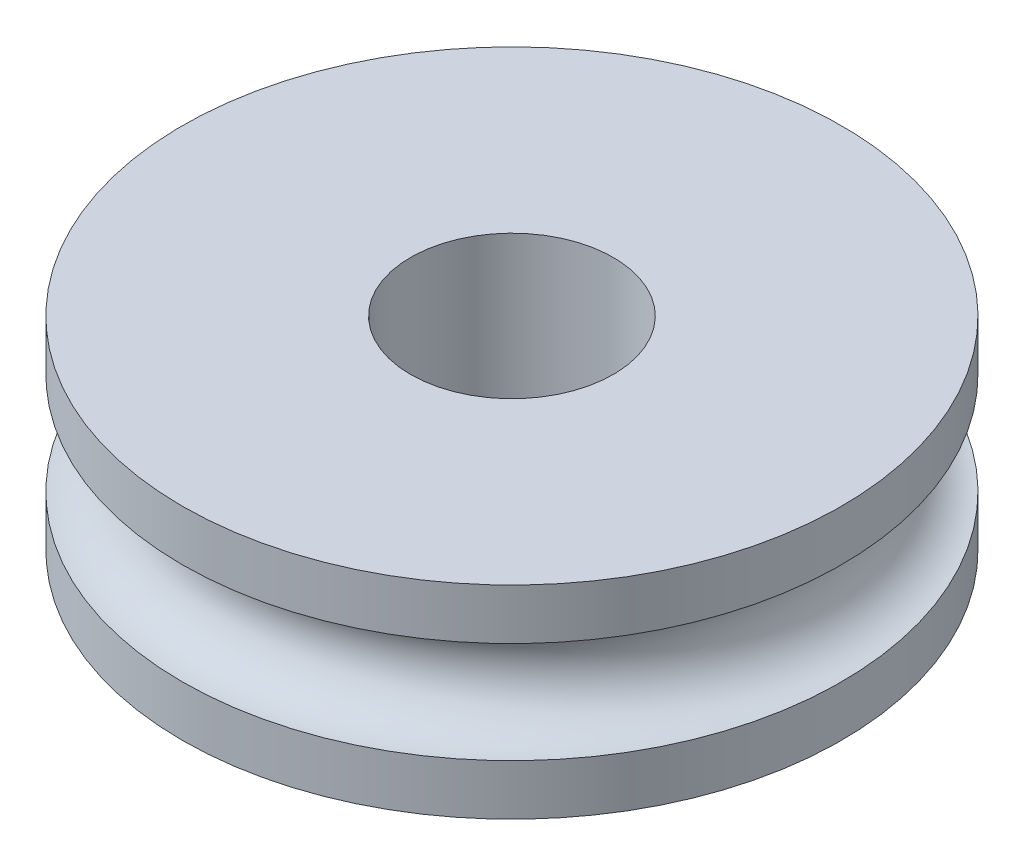
SolidWorks part; units mm, degrees
ref_plane "Front Plane" through (0, 0, 0) normal (0, 0, 1) x (1, 0, 0)
ref_plane "Top Plane" through (0, 0, 0) normal (0, 1, 0) x (1, 0, 0)
ref_plane "Right Plane" through (0, 0, 0) normal (1, 0, 0) x (0, 0, -1)
sketch "Sketch1" plane through (0, 0, 0) normal (0, 0, 1) x (1, 0, 0)
  line L0 (0, 2) -> (0, -2) construction
  line L1 (2, 2) -> (2, -2)
  line L2 (2, -2) -> (6.5, -2)
  line L3 (6.5, -2) -> (6.5, -1)
  line L4 (6.5, 1) -> (6.5, 2)
  line L5 (6.5, 2) -> (2, 2)
  line L6 (2, 0) -> (6.5, 0) construction
  line L7 (0, 0) -> (2, 0) construction
  arc A0 (6.5, -1) -> (6.5, 1) centre (6.5, 0) cw
  point P4 (0, 0)
  point P14 (0, 0)
  point P15 (3.1872, 0)
  dimension "D3" = 1
  dimension "D1" = 4
  dimension "D2" = 4
  dimension "D4" = 13
  dimension "D5" = 4
revolve "Revolve1" add sketch "Sketch1" angle 360 about L0
